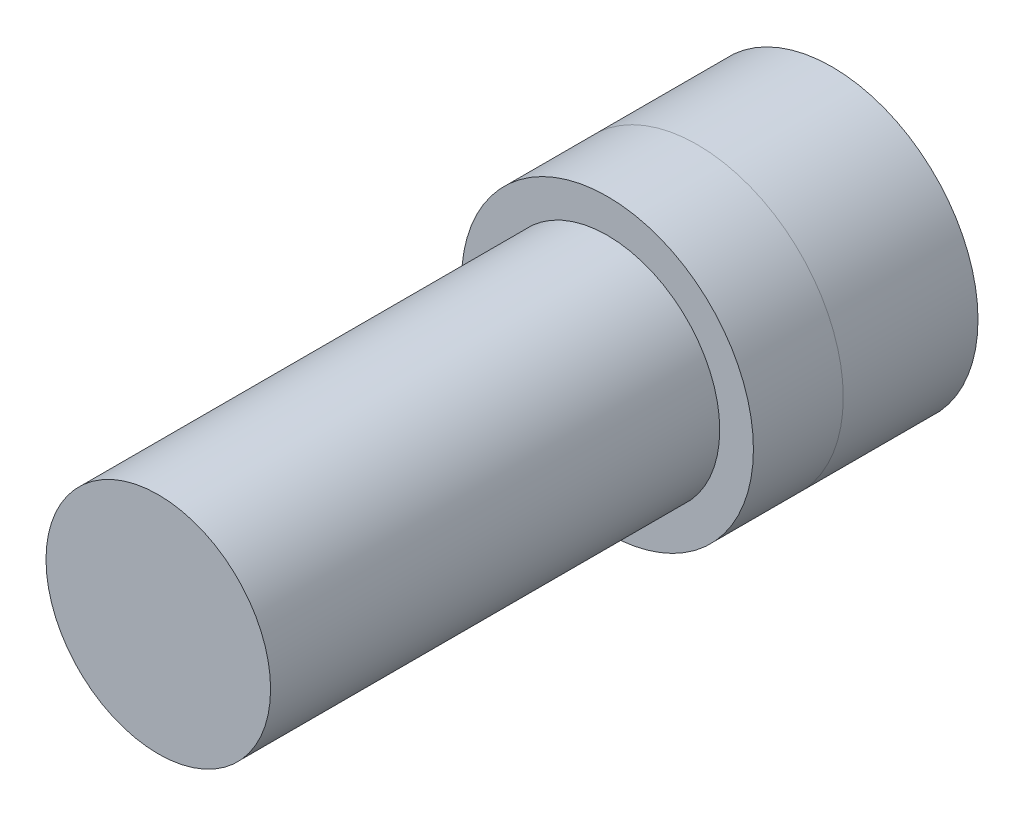
SolidWorks part; units mm, degrees
ref_plane "Plan de face" through (0, 0, 0) normal (0, 0, 1) x (1, 0, 0)
ref_plane "Plan de dessus" through (0, 0, 0) normal (0, 1, 0) x (1, 0, 0)
ref_plane "Plan de droite" through (0, 0, 0) normal (1, 0, 0) x (0, 0, -1)
sketch "Esquisse1" plane through (0, 0, 0) normal (0, 0, 1) x (1, 0, 0)
  circle A0 centre (0, 0) radius 6.5
  dimension "D1" = 13
extrude "Boss.-Extru.1" add sketch "Esquisse1" along normal blind 10
sketch "Esquisse2" plane through (0, 0, 10) normal (0, 0, 1) x (1, 0, 0)
  circle A0 centre (0, 0) radius 5
  dimension "D1" = 10
extrude "Boss.-Extru.2" add sketch "Esquisse2" along normal blind 20
sketch "Esquisse3" plane through (0, 0, 0) normal (0, 0, -1) x (-1, 0, 0)
  circle A0 centre (0, 0) radius 6.5
  dimension "D1" = 13
extrude "Enlèv. mat.-Extru.1" cut sketch "Esquisse3" against normal blind 6
sketch "Esquisse5" plane through (0, 0, 6) normal (0, 0, -1) x (-1, 0, 0)
  circle A0 centre (0, 0) radius 6.5
extrude "Boss.-Extru.4" add sketch "Esquisse5" along normal blind 6 separate body
